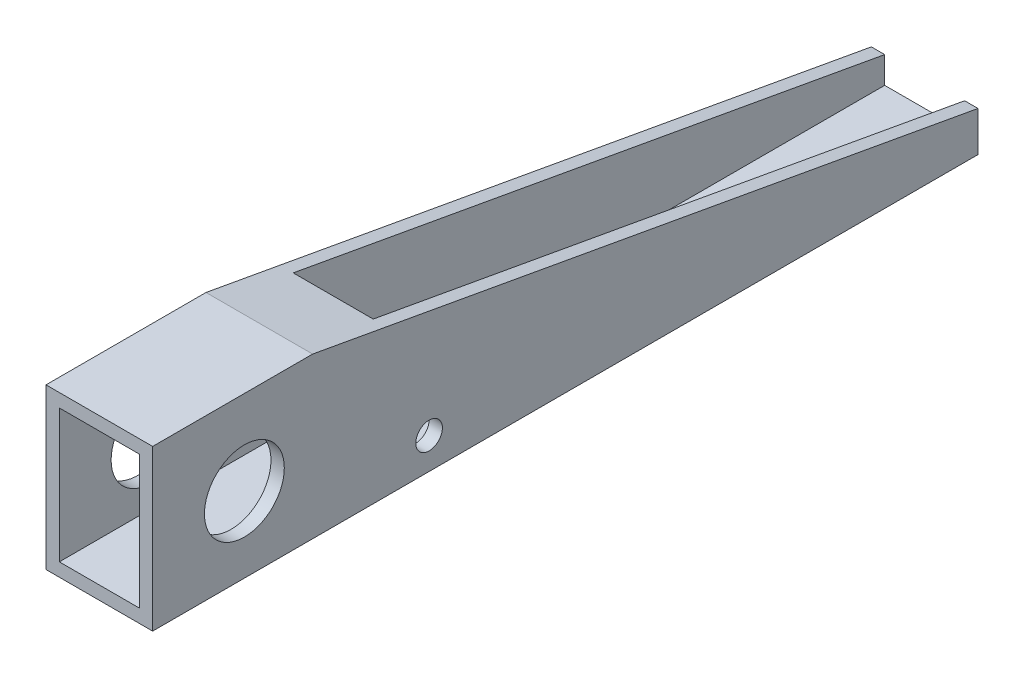
SolidWorks part; units mm, degrees
ref_plane "Front Plane" through (0, 0, 0) normal (0, 0, 1) x (1, 0, 0)
ref_plane "Top Plane" through (0, 0, 0) normal (0, 1, 0) x (1, 0, 0)
ref_plane "Right Plane" through (0, 0, 0) normal (1, 0, 0) x (0, 0, -1)
sketch "Sketch1" plane through (0, 0, 0) normal (0, 0, 1) x (1, 0, 0)
  line L1 (0, 0) -> (3.175, 0)
  line L2 (0, 0) -> (0, 38.1)
  line L3 (0, 38.1) -> (3.175, 38.1)
  line L4 (3.175, 0) -> (3.175, 38.1)
  line L5 (3.175, 0) -> (22.225, 0)
  line L6 (3.175, 0) -> (3.175, 3.175)
  line L7 (3.175, 3.175) -> (22.225, 3.175)
  line L8 (22.225, 0) -> (22.225, 3.175)
  line L9 (22.225, 0) -> (25.4, 0)
  line L10 (22.225, 0) -> (22.225, 38.1)
  line L11 (22.225, 38.1) -> (25.4, 38.1)
  line L12 (25.4, 0) -> (25.4, 38.1)
  line L13 (22.225, 38.1) -> (3.175, 38.1)
  line L14 (22.225, 38.1) -> (22.225, 34.925)
  line L15 (22.225, 34.925) -> (3.175, 34.925)
  line L16 (3.175, 38.1) -> (3.175, 34.925)
  dimension "D1" = 38.1
  dimension "D2" = 25.4
  dimension "D3" = 3.175
  dimension "D4" = 3.175
  dimension "D5" = 3.175
  dimension "D6" = 3.175
extrude "Boss-Extrude1" add sketch "Sketch1" along normal blind 196.5706 contours L1 L4 L3 L2 | L5 L8 L7 L4 | L9 L12 L11 L10 L8 | L15 L10 L13 L4
sketch "Sketch2" plane through (25.4, 0, 0) normal (1, 0, 0) x (0, 0, -1)
  line L0 (-196.5706, 0) -> (-196.5706, 38.1) construction
  line L1 (-196.5706, 38.1) -> (0, 38.1) construction
  line L2 (-196.5706, 38.1) -> (0, 38.1) construction
  line L3 (0, 0) -> (0, 38.1) construction
  line L4 (0, 38.1) -> (0, 0) construction
  line L5 (0, 0) -> (-196.5706, 0) construction
  line L6 (-196.5706, 3.175) -> (0, 3.175) construction
  line L7 (-98.2853, 3.175) -> (-98.2853, 38.1) construction
  line L8 (-196.5706, 19.05) -> (0, 9.525) construction
  line L9 (-158.4706, 38.1) -> (0, 9.525)
  line L10 (-158.4706, 38.1) -> (0, 38.1)
  line L11 (0, 38.1) -> (0, 9.525)
  circle A0 centre (-174.7266, 17.9915) radius 9.5123
  circle A1 centre (-143.0138, 16.4549) radius 6.35 construction
  circle A2 centre (-117.6436, 15.2255) radius 6.35 construction
  circle A3 centre (-92.2733, 13.9962) radius 6.35 construction
  circle A4 centre (-130.7364, 7.4258) radius 3.175
  point P17 (-98.2853, 20.6375)
  point P22 (-158.4706, 38.1)
  point P33 (0, 9.525)
  dimension "D2" = 19.0246
  dimension "D4" = 12.7
  dimension "D9" = 12.7
  dimension "D11" = 12.7
  dimension "D14" = 6.35
  dimension "D1" = 3.175
  dimension "D3" = 21.844
  dimension "D5" = 31.75
  dimension "D7" = 38.1
  dimension "D8" = 6.35
  dimension "D6" = 25.4
  dimension "D10" = 25.4
  dimension "D15" = 15.24
  dimension "D16" = 15.24
extrude "Side cut" cut sketch "Sketch2" against normal through all
